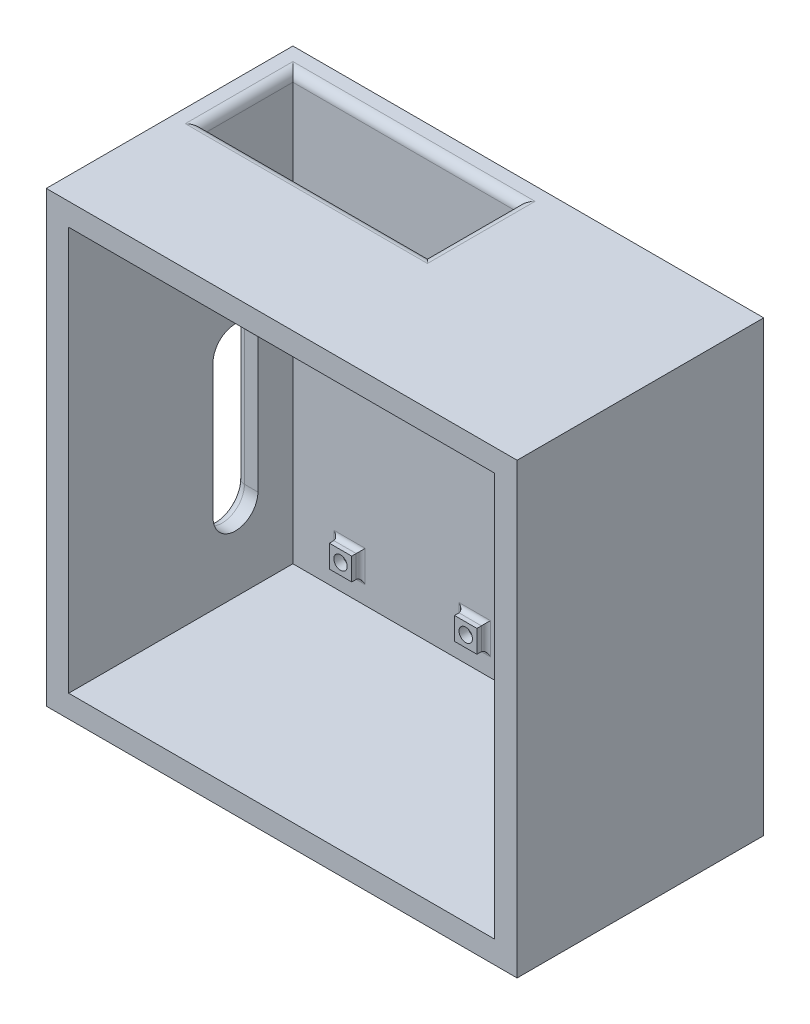
SolidWorks part; units mm, degrees
ref_plane "Front Plane" through (0, 0, 0) normal (0, 0, 1) x (1, 0, 0)
ref_plane "Top Plane" through (0, 0, 0) normal (0, 1, 0) x (1, 0, 0)
ref_plane "Right Plane" through (0, 0, 0) normal (1, 0, 0) x (0, 0, -1)
sketch "Sketch1" plane through (0, 0, 0) normal (0, 0, 1) x (1, 0, 0)
  line L1 (0, 0) -> (20, 0)
  line L2 (0, 0) -> (0, 40)
  line L3 (0, 40) -> (20, 40)
  line L4 (20, 0) -> (20, 40)
  line L5 (-65, 70) -> (40, 70)
  line L6 (-65, 70) -> (-65, -30)
  line L7 (-65, -30) -> (40, -30)
  line L8 (40, 70) -> (40, -30)
  point P9 (20, 20)
  dimension "D1" = 20
  dimension "D2" = 40
  dimension "D3" = 30
  dimension "D4" = 30
  dimension "D5" = 20
  dimension "D6" = 65
extrude "Boss-Extrude1" add sketch "Sketch1" along normal blind 5
sketch "Sketch2" plane through (0, 0, 5) normal (0, 0, 1) x (1, 0, 0)
  line L0 (-60, 65) -> (-60, -25)
  line L1 (-65, 70) -> (40, 70)
  line L2 (-65, 70) -> (-65, -30)
  line L3 (-65, -30) -> (40, -30)
  line L4 (40, 70) -> (40, -30)
  line L5 (-60, -25) -> (35, -25)
  line L6 (35, 65) -> (35, -25)
  line L7 (-60, 65) -> (35, 65)
  dimension "D1" = 5
extrude "Boss-Extrude2" add sketch "Sketch2" along normal blind 50
sketch "Sketch3" plane through (0, 0, 5) normal (0, 0, 1) x (1, 0, 0)
  line L0 (-60, -25) -> (35, -25) construction
  line L1 (-55, 48.58) -> (-1.66, 48.58)
  line L2 (-55, 48.58) -> (-55, -20)
  line L3 (-55, -20) -> (-1.66, -20)
  line L4 (-1.66, 48.58) -> (-1.66, -20)
  line L5 (-60, 65) -> (-60, -25) construction
  circle A0 centre (-47.38, -17.46) radius 1.5
  circle A1 centre (-19.46, -17.46) radius 1.5
  circle A2 centre (-52.46, 34.61) radius 1.5
  circle A3 centre (-4.2, 33.34) radius 1.5
  dimension "D5" = 3
  dimension "D6" = 2.54
  dimension "D7" = 7.62
  dimension "D8" = 27.92
  dimension "D9" = 3
  dimension "D10" = 2.54
  dimension "D11" = 3
  dimension "D12" = 2.54
  dimension "D13" = 13.97
  dimension "D14" = 3
  dimension "D15" = 15.24
  dimension "D16" = 2.54
  dimension "D1" = 53.34
  dimension "D2" = 68.58
  dimension "D3" = 5
  dimension "D4" = 5
sketch "Sketch4" plane through (0, 0, 5) normal (0, 0, 1) x (1, 0, 0)
  line L1 (-54.96, 37.11) -> (-49.96, 37.11)
  line L2 (-54.96, 37.11) -> (-54.96, 32.11)
  line L3 (-54.96, 32.11) -> (-49.96, 32.11)
  line L4 (-49.96, 37.11) -> (-49.96, 32.11)
  line L5 (-54.96, 37.11) -> (-49.96, 32.11) construction
  line L6 (-54.96, 32.11) -> (-49.96, 37.11) construction
  line L7 (-6.7, 35.84) -> (-1.7, 35.84)
  line L8 (-6.7, 35.84) -> (-6.7, 30.84)
  line L9 (-6.7, 30.84) -> (-1.7, 30.84)
  line L10 (-1.7, 35.84) -> (-1.7, 30.84)
  line L11 (-6.7, 35.84) -> (-1.7, 30.84) construction
  line L12 (-6.7, 30.84) -> (-1.7, 35.84) construction
  line L13 (-49.88, -14.96) -> (-44.88, -14.96)
  line L14 (-49.88, -14.96) -> (-49.88, -19.96)
  line L15 (-49.88, -19.96) -> (-44.88, -19.96)
  line L16 (-44.88, -14.96) -> (-44.88, -19.96)
  line L17 (-49.88, -14.96) -> (-44.88, -19.96) construction
  line L18 (-49.88, -19.96) -> (-44.88, -14.96) construction
  line L19 (-21.96, -19.96) -> (-16.96, -19.96)
  line L20 (-21.96, -19.96) -> (-21.96, -14.96)
  line L21 (-21.96, -14.96) -> (-16.96, -14.96)
  line L22 (-16.96, -19.96) -> (-16.96, -14.96)
  line L23 (-21.96, -19.96) -> (-16.96, -14.96) construction
  line L24 (-21.96, -14.96) -> (-16.96, -19.96) construction
  circle A1 centre (-4.2, 33.34) radius 1.5
  circle A2 centre (-19.46, -17.46) radius 1.5
  circle A3 centre (-47.38, -17.46) radius 1.5
  circle A4 centre (-52.46, 34.61) radius 1.5
  point P0 (-52.46, 34.61)
  point P6 (-4.2, 33.34)
  point P12 (-47.38, -17.46)
  point P18 (-19.46, -17.46)
  dimension "D1" = 5
  dimension "D2" = 5
  dimension "D3" = 5
  dimension "D4" = 5
  dimension "D5" = 5
  dimension "D6" = 5
  dimension "D7" = 5
  dimension "D8" = 5
extrude "Boss-Extrude3" add sketch "Sketch4" along normal blind 2
fillet "Fillet1" radius 1 16 edges at (-19.46, -14.96, 5) (-21.96, -17.46, 5) (-47.38, -14.96, 5) (-49.88, -17.46, 5) (-44.88, -17.46, 5) (-47.38, -19.96, 5) (-16.96, -17.46, 5) (-19.46, -19.96, 5) (-4.2, 30.84, 5) (-6.7, 33.34, 5) (-1.7, 33.34, 5) (-4.2, 35.84, 5) (-52.46, 37.11, 5) (-52.46, 32.11, 5) (-49.96, 34.61, 5) (-54.96, 34.61, 5)
sketch "Sketch5" plane through (0, 70, 0) normal (0, 1, 0) x (1, 0, 0)
  line L0 (40, 0) -> (-65, 0) construction
  line L1 (-60, -5) -> (-10, -5)
  line L2 (-60, -5) -> (-60, -25)
  line L3 (-60, -25) -> (-10, -25)
  line L4 (-10, -5) -> (-10, -25)
  line L5 (-65, -55) -> (-65, 0) construction
  dimension "D1" = 5
  dimension "D2" = 5
  dimension "D3" = 20
  dimension "D4" = 50
extrude "Cut-Extrude1" cut sketch "Sketch5" against normal blind 5
sketch "Sketch6" plane through (-65, 0, 0) normal (-1, 0, 0) x (0, 0, 1)
  line L0 (17.8053, 22.7559) -> (17.8053, -7.2441) construction
  line L1 (22.8053, 22.7559) -> (22.8053, -7.2441)
  line L2 (12.8053, 22.7559) -> (12.8053, -7.2441)
  arc A0 (22.8053, 22.7559) -> (12.8053, 22.7559) centre (17.8053, 22.7559) ccw
  arc A1 (12.8053, -7.2441) -> (22.8053, -7.2441) centre (17.8053, -7.2441) ccw
  point P2 (17.8053, 7.7559)
  dimension "D1" = 5
  dimension "D2" = 30
extrude "Cut-Extrude2" cut sketch "Sketch6" against normal blind 5
fillet "Fillet2" radius 2 4 edges at (-65, -12.2441, 17.8053) (-65, 7.7559, 12.8053) (-65, 27.7559, 17.8053) (-65, 7.7559, 22.8053)
fillet "Fillet3" radius 2 4 edges at (-35, 70, 5) (-60, 70, 15) (-35, 70, 25) (-10, 70, 15)
